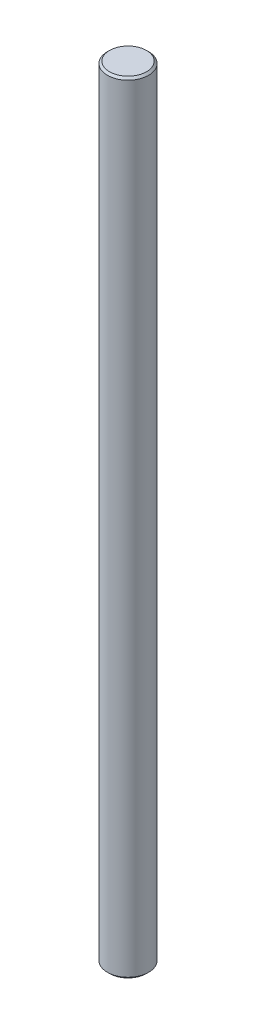
SolidWorks part; units mm, degrees
ref_plane "Front Plane" through (0, 0, 0) normal (0, 0, 1) x (1, 0, 0)
ref_plane "Top Plane" through (0, 0, 0) normal (0, 1, 0) x (1, 0, 0)
ref_plane "Right Plane" through (0, 0, 0) normal (1, 0, 0) x (0, 0, -1)
ref_plane "Plane4" through (0, 0, 4.9351) normal (0, 0, 1) x (1, 0, 0)
sketch "Sketch1" plane through (0, 0, 4.9351) normal (0, 0, 1) x (1, 0, 0)
  line L0 (-1.1444, 12.6121) -> (-2.0444, 12.6121)
  line L1 (-2.0444, 12.6121) -> (-2.0444, -25.3879)
  line L2 (-2.0444, -25.3879) -> (-1.1444, -25.3879)
  line L3 (-1.1444, -25.3879) -> (-1.0444, -25.2879)
  line L4 (-1.0444, -25.2879) -> (-1.0444, 12.5121)
  line L5 (-1.0444, 12.5121) -> (-1.1444, 12.6121)
  line L6 (-2.0444, 12.6121) -> (-2.0444, -25.3879) construction
revolve "Revolve1" add sketch "Sketch1" angle 360 about L6
